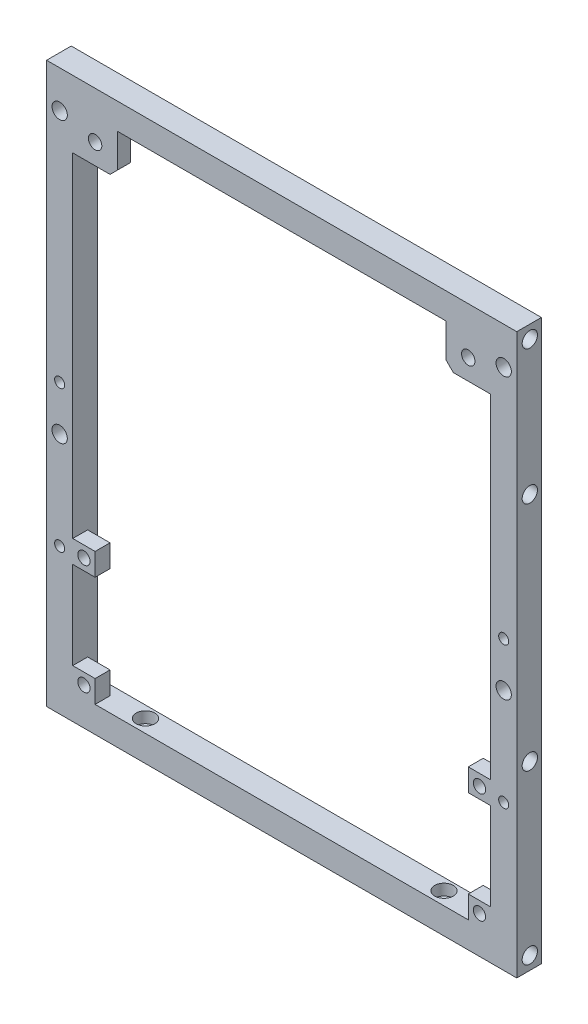
SolidWorks part; units mm, degrees
ref_plane "Front Plane" through (0, 0, 0) normal (0, 0, 1) x (1, 0, 0)
ref_plane "Top Plane" through (0, 0, 0) normal (0, 1, 0) x (1, 0, 0)
ref_plane "Right Plane" through (0, 0, 0) normal (1, 0, 0) x (0, 0, -1)
sketch "Sketch1" plane through (0, 0, 0) normal (0, 0, 1) x (1, 0, 0)
  line L1 (-63, -75) -> (63, -75)
  line L2 (-63, -75) -> (-63, 75)
  line L3 (-63, 75) -> (63, 75)
  line L4 (63, -75) -> (63, 75)
  line L5 (-63, -75) -> (63, 75) construction
  line L6 (-63, 75) -> (63, -75) construction
  line L7 (-56, -68) -> (56, -68)
  line L8 (-56, -68) -> (-56, 68)
  line L9 (-56, 68) -> (56, 68)
  line L10 (56, -68) -> (56, 68)
  line L11 (-56, -68) -> (56, 68) construction
  line L12 (-56, 68) -> (56, -68) construction
  point P0 (0, 0)
  point P6 (0, 0)
  dimension "D1" = 126
  dimension "D2" = 150
  dimension "D3" = 7
  dimension "D4" = 7
extrude "Boss-Extrude1" add sketch "Sketch1" along normal blind 7
sketch "Sketch2" plane through (-63, 0, 0) normal (-1, 0, 0) x (0, 0, 1)
  line L0 (3.5, 71.5) -> (3.5, -71.5) construction
  line L1 (7, 75) -> (0, 75) construction
  circle A0 centre (3.5, -71.5) radius 2.05
  circle A2 centre (3.5, 71.5) radius 2.05
  circle A3 centre (3.5, 35.5) radius 2.05
  circle A4 centre (3.5, -26.5) radius 2.05
  point P2 (3.5, 0)
  point P7 (3.5, 75)
  dimension "D2" = 4.1
  dimension "D3" = 36
  dimension "D4" = 45
  dimension "D1" = 3.5
extrude "Cut-Extrude1" cut sketch "Sketch2" against normal blind 6
mirror "Mirror1" about plane through (0, 0, 0) normal (1, 0, 0) of "Cut-Extrude1"
sketch "Sketch3" plane through (0, -68, 0) normal (0, 1, 0) x (1, 0, 0)
  line L0 (0, 0) -> (0, -7) construction
  line L1 (-56, 0) -> (56, 0) construction
  line L2 (-56, -7) -> (56, -7) construction
  line L3 (40, -3.5) -> (-40, -3.5) construction
  circle A0 centre (40, -3.5) radius 1.35
  circle A1 centre (-40, -3.5) radius 1.35
  point P9 (0, -3.5)
  dimension "D1" = 2.7
  dimension "D2" = 80
extrude "Cut-Extrude2" cut sketch "Sketch3" against normal through all
sketch "Sketch4" plane through (0, -68, 0) normal (0, 1, 0) x (1, 0, 0)
  circle A0 centre (40, -3.5) radius 2.5
  circle A1 centre (-40, -3.5) radius 2.5
  dimension "D1" = 5
extrude "Cut-Extrude3" cut sketch "Sketch4" against normal blind 3
sketch "Sketch5" plane through (0, 0, 0) normal (0, 0, -1) x (-1, 0, 0)
  line L0 (-59.5, -75) -> (-59.5, 75) construction
  line L1 (63, -75) -> (-63, -75) construction
  line L2 (-63, 75) -> (63, 75) construction
  line L3 (-56, 0) -> (-63, 0) construction
  line L4 (-56, -68) -> (-56, 68) construction
  line L5 (-63, -75) -> (-63, 75) construction
  line L6 (0, 75) -> (0, -75) construction
  line L7 (56, -68) -> (-56, -68) construction
  circle A0 centre (-59.5, 2) radius 1.35
  circle A1 centre (59.5, 2) radius 1.35
  circle A2 centre (-59.5, -36) radius 1.35
  circle A3 centre (59.5, -36) radius 1.35
  point P12 (-59.5, 0)
  point P13 (-59.5, 0)
  dimension "D1" = 2.7
  dimension "D2" = 2
  dimension "D3" = 32
extrude "Cut-Extrude4" cut sketch "Sketch5" against normal through all
sketch "Sketch6" plane through (0, 0, 0) normal (0, 0, -1) x (-1, 0, 0)
  circle A0 centre (-59.5, 2) radius 2.5
  circle A1 centre (59.5, 2) radius 2.5
  circle A2 centre (-59.5, -36) radius 2.5
  circle A3 centre (59.5, -36) radius 2.5
  dimension "D1" = 5
extrude "Cut-Extrude5" cut sketch "Sketch6" against normal blind 3
sketch "Sketch7" plane through (0, 0, 0) normal (0, 0, -1) x (-1, 0, 0)
  line L0 (-56, 68) -> (-63, 68) construction
  line L1 (-63, -75) -> (-63, 75) construction
  line L2 (-59.5, 65) -> (-59.5, -10) construction
  line L3 (-63, 75) -> (63, 75) construction
  circle A0 centre (-59.5, 65) radius 2.05
  circle A1 centre (-59.5, -10) radius 2.05
  point P8 (-59.5, 68)
  dimension "D1" = 4.1
  dimension "D2" = 10
  dimension "D3" = 75
extrude "Cut-Extrude6" cut sketch "Sketch7" against normal through all
mirror "Mirror2" about plane through (0, 0, 0) normal (1, 0, 0) of "Cut-Extrude6"
sketch "Sketch8" plane through (0, 0, 3) normal (0, 0, -1) x (-1, 0, 0)
  line L2 (-60.85, -0.1042) -> (-60.85, 4.1042)
  line L4 (-58.15, -0.1042) -> (-58.15, 4.1042)
  line L5 (-60.85, -0.1042) -> (-58.15, 4.1042) construction
  line L6 (-60.85, 4.1042) -> (-58.15, -0.1042) construction
  line L8 (-60.85, -38.1042) -> (-60.85, -33.8958)
  line L10 (-58.15, -38.1042) -> (-58.15, -33.8958)
  line L11 (-60.85, -38.1042) -> (-58.15, -33.8958) construction
  line L12 (-60.85, -33.8958) -> (-58.15, -38.1042) construction
  circle A0 centre (-59.5, 2) radius 2.5 construction
  circle A1 centre (-59.5, -36) radius 2.5 construction
  circle A2 centre (-59.5, -36) radius 2.5 construction
  arc A3 (-58.15, 4.1042) -> (-60.85, 4.1042) centre (-59.5, 2) ccw
  arc A4 (-58.15, -33.8958) -> (-60.85, -33.8958) centre (-59.5, -36) ccw
  circle A5 centre (-59.5, 2) radius 1.35 construction
  circle A6 centre (-59.5, -36) radius 1.35 construction
  arc A7 (-60.85, -38.1042) -> (-58.15, -38.1042) centre (-59.5, -36) ccw
  arc A8 (-60.85, -0.1042) -> (-58.15, -0.1042) centre (-59.5, 2) ccw
  point P0 (-59.5, 2)
  point P8 (-59.5, -36)
extrude "Cut-Extrude7" cut sketch "Sketch8" against normal blind 0.2
sketch "Sketch9" plane through (0, 0, 3.2) normal (0, 0, -1) x (-1, 0, 0)
  line L0 (-58.15, 2) -> (-58.15, 4.1042) construction
  line L1 (-60.85, 0.65) -> (-58.15, 0.65)
  line L2 (-60.85, 0.65) -> (-60.85, 3.35)
  line L3 (-60.85, 3.35) -> (-58.15, 3.35)
  line L4 (-58.15, 0.65) -> (-58.15, 3.35)
  line L5 (-60.85, 0.65) -> (-58.15, 3.35) construction
  line L6 (-60.85, 3.35) -> (-58.15, 0.65) construction
  line L7 (-58.15, -38.1042) -> (-58.15, -33.8958) construction
  line L8 (-60.85, -37.35) -> (-58.15, -37.35)
  line L9 (-60.85, -37.35) -> (-60.85, -34.65)
  line L10 (-60.85, -34.65) -> (-58.15, -34.65)
  line L11 (-58.15, -37.35) -> (-58.15, -34.65)
  line L12 (-60.85, -37.35) -> (-58.15, -34.65) construction
  line L13 (-60.85, -34.65) -> (-58.15, -37.35) construction
  arc A0 (-58.15, 2) -> (-60.85, 2) centre (-59.5, 2) ccw construction
  point P0 (-59.5, 2)
  point P8 (-59.5, -36)
extrude "Cut-Extrude8" cut sketch "Sketch9" against normal blind 0.2
mirror "Mirror3" about plane through (0, 0, 0) normal (1, 0, 0) of "Cut-Extrude8", "Cut-Extrude7"
sketch "Sketch10" plane through (0, 0, 7) normal (0, 0, 1) x (1, 0, 0)
  line L0 (56, -68) -> (56, 68) construction
  line L1 (56, -68) -> (50, -68)
  line L2 (56, -68) -> (56, -62)
  line L3 (56, -62) -> (50, -62)
  line L4 (50, -68) -> (50, -62)
  line L5 (56, -38.5) -> (50, -38.5)
  line L6 (56, -38.5) -> (56, -32.5)
  line L7 (56, -32.5) -> (50, -32.5)
  line L8 (50, -38.5) -> (50, -32.5)
  line L9 (-56, -68) -> (56, -68) construction
  dimension "D1" = 6
  dimension "D2" = 35.5
extrude "Boss-Extrude2" add sketch "Sketch10" against normal offset from surface (4 mm away) 3 up to face at (-57.45, -10, 0)
sketch "Sketch11" plane through (0, 0, 3) normal (0, 0, -1) x (-1, 0, 0)
  line L0 (-56, -38.5) -> (-50, -32.5) construction
  line L2 (-56, -68) -> (-50, -62) construction
  circle A0 centre (-53, -35.5) radius 1.65
  circle A1 centre (-53, -65) radius 1.65
  dimension "D1" = 3.3
extrude "Cut-Extrude9" cut sketch "Sketch11" against normal through all
mirror "Mirror4" about plane through (0, 0, 0) normal (1, 0, 0) of "Cut-Extrude9", "Boss-Extrude2"
chamfer "Chamfer1" distance 0.4 angle 45 4 edges at (-56, 0, 0) (0, 68, 0) (56, 0, 0) (0, -68, 0)
chamfer "Chamfer2" distance 0.4 angle 45 4 edges at (0, 75, 0) (-63, 0, 0) (0, -75, 0) (63, 0, 0)
sketch "Skizze2" plane through (0, 0, 7) normal (0, 0, 1) x (1, 0, 0)
  line L0 (0, 68) -> (0, -68) construction
  line L1 (56, 68) -> (-56, 68) construction
  line L2 (-50, -68) -> (50, -68) construction
  line L3 (-56, -68) -> (-56, 68) construction
  line L5 (-56, 68) -> (-56, 57)
  line L8 (-56, 62.5) -> (56, 62.5) construction
  line L9 (-44, 68) -> (-44, 57)
  line L10 (-44, 57) -> (-56, 57)
  line L11 (-44, 57) -> (-56, 68) construction
  line L12 (56, 68) -> (56, -68) construction
  line L13 (-44, 68) -> (-56, 68)
  line L16 (44, 68) -> (44, 57)
  line L17 (44, 57) -> (56, 57)
  line L18 (56, 68) -> (56, 57)
  line L19 (44, 68) -> (56, 68)
  circle A0 centre (-50, 62.5) radius 1.8
  circle A2 centre (50, 62.5) radius 1.8
  dimension "D4" = 3.6
  dimension "D1" = 0
  dimension "D2" = 11
  dimension "D3" = 12
extrude "Aufsatz-Linear austragen1" add sketch "Skizze2" against normal blind 4
chamfer "Fase1" distance 2 angle 45 2 edges at (-44, 57, 5) (44, 57, 5)
chamfer "Fase2" distance 0.5 angle 45 6 edges at (-44, 63.5, 3) (-45, 58, 3) (-51, 57, 3) (51, 57, 3) (44, 63.5, 3) (45, 58, 3)
